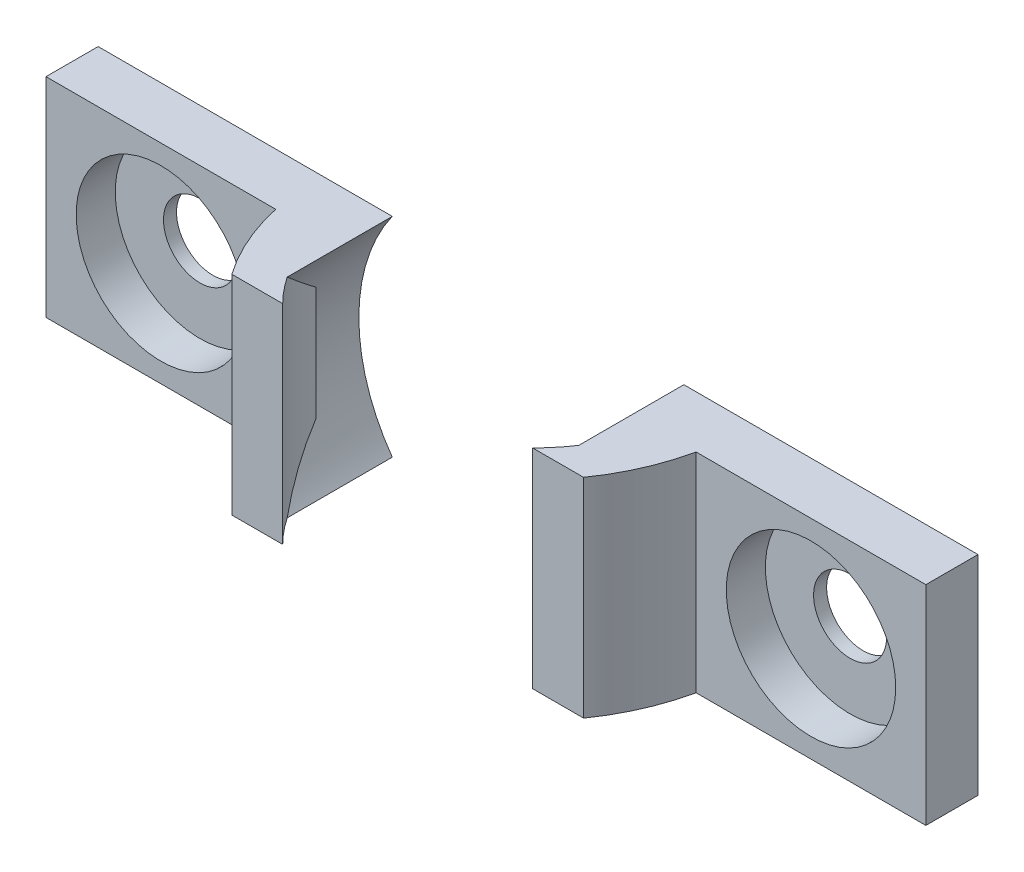
SolidWorks part; units mm, degrees
ref_plane "Alzado" through (0, 0, 0) normal (0, 0, 1) x (1, 0, 0)
ref_plane "Planta" through (0, 0, 0) normal (0, 1, 0) x (1, 0, 0)
ref_plane "Vista lateral" through (0, 0, 0) normal (1, 0, 0) x (0, 0, -1)
sketch "Croquis1" plane through (0, 0, 0) normal (0, 0, 1) x (1, 0, 0)
  line L0 (-52.0193, 52.8694) -> (-52.0193, 39.1194) construction
  line L1 (-58.8943, 45.9944) -> (-45.1443, 45.9944) construction
  line L2 (-57.6108, 41.9944) -> (-46.4277, 41.9944)
  line L3 (-57.6108, 49.9944) -> (-46.4277, 49.9944)
  line L4 (-58.8943, 49.9944) -> (-45.1443, 49.9944) construction
  line L5 (-58.8943, 41.9944) -> (-45.1443, 41.9944) construction
  line L6 (-57.6108, 41.9944) -> (-68.8943, 41.9944)
  line L7 (-68.8943, 41.9944) -> (-68.8943, 49.9944)
  line L9 (-68.8943, 49.9944) -> (-57.6108, 49.9944)
  line L10 (-46.4277, 41.9944) -> (-35.1443, 41.9944)
  line L11 (-35.1443, 41.9944) -> (-35.1443, 49.9944)
  line L12 (-35.1443, 49.9944) -> (-46.4277, 49.9944)
  circle A0 centre (-52.0193, 45.9944) radius 6.875 construction
  circle A1 centre (-52.0193, 45.9944) radius 6.875
  dimension "D3" = 10
  dimension "D1" = 4
  dimension "D2" = 4
extrude "Saliente-Extruir1" add sketch "Croquis1" along normal blind 2 contours A1 L9 L7 L6 | A1 L10 L11 L12
ref_plane "Plano1" through (0, 45.9944, 0) normal (0, -1, 0) x (-1, 0, 0)
sketch "Croquis2" plane through (0, 45.9944, 0) normal (0, -1, 0) x (-1, 0, 0)
  line L0 (35.1443, -2) -> (46.4277, -2) construction
  line L1 (43.957, -2) -> (45.5001, -2)
  line L2 (68.8943, -2) -> (57.6108, -2) construction
  line L3 (60.0815, -2) -> (58.5385, -2)
  line L4 (52.0193, -7) -> (46.0193, -7)
  line L5 (58.7646, -5) -> (56.8151, -5)
  line L6 (52.0193, 1.75) -> (52.0193, -1.5) construction
  line L7 (45.2739, -5) -> (47.2234, -5)
  line L8 (68.8943, 0) -> (57.6108, 0) construction
  line L9 (68.8943, 0) -> (57.6108, 0)
  circle A2 centre (52.0193, -0.25) radius 8.25
  circle A6 centre (52.0193, -0.25) radius 6.75
  dimension "D2" = 3
  dimension "D4" = 13.5
  dimension "D5" = 7
  dimension "D1" = 1.5
extrude "Saliente-Extruir2" add sketch "Croquis2" along normal mid plane 8
sketch "Croquis3" plane through (0, 0, 2) normal (0, 0, 1) x (1, 0, 0)
  line L2 (-58.5385, 49.9944) -> (-58.5385, 48.1774)
  line L3 (-57.6108, 49.9944) -> (-58.5385, 49.9944)
  line L5 (-57.6108, 49.9944) -> (-58.5385, 49.9944)
  line L7 (-58.5385, 49.9944) -> (-58.5385, 48.1774)
  arc A1 (-57.6108, 49.9944) -> (-58.5385, 48.1774) centre (-52.0193, 45.9944) ccw
  arc A2 (-57.6108, 49.9944) -> (-58.5385, 48.1774) centre (-52.0193, 45.9944) ccw
  dimension "D1" = 0
extrude "Saliente-Extruir3" add sketch "Croquis3" along normal up to next
sketch "Croquis4" plane through (0, 0, 2) normal (0, 0, 1) x (1, 0, 0)
  line L2 (-45.5001, 48.1774) -> (-45.5001, 49.9944)
  line L3 (-45.5001, 49.9944) -> (-46.4277, 49.9944)
  line L5 (-45.5001, 49.9944) -> (-46.4277, 49.9944)
  line L7 (-45.5001, 48.1774) -> (-45.5001, 49.9944)
  arc A1 (-45.5001, 48.1774) -> (-46.4277, 49.9944) centre (-52.0193, 45.9944) ccw
  arc A2 (-45.5001, 48.1774) -> (-46.4277, 49.9944) centre (-52.0193, 45.9944) ccw
  dimension "D1" = 0
extrude "Saliente-Extruir4" add sketch "Croquis4" along normal up to next
sketch "Croquis5" plane through (0, 0, 2) normal (0, 0, 1) x (1, 0, 0)
  line L2 (-58.5385, 43.8114) -> (-58.5385, 41.9944)
  line L3 (-58.5385, 41.9944) -> (-57.6108, 41.9944)
  line L5 (-58.5385, 41.9944) -> (-57.6108, 41.9944)
  line L7 (-58.5385, 43.8114) -> (-58.5385, 41.9944)
  arc A1 (-58.5385, 43.8114) -> (-57.6108, 41.9944) centre (-52.0193, 45.9944) ccw
  arc A2 (-58.5385, 43.8114) -> (-57.6108, 41.9944) centre (-52.0193, 45.9944) ccw
  dimension "D1" = 0
extrude "Saliente-Extruir5" add sketch "Croquis5" along normal up to next
sketch "Croquis6" plane through (0, 0, 2) normal (0, 0, 1) x (1, 0, 0)
  line L2 (-46.4277, 41.9944) -> (-45.5001, 41.9944)
  line L3 (-45.5001, 41.9944) -> (-45.5001, 43.8114)
  line L4 (-46.4277, 41.9944) -> (-45.5001, 41.9944)
  line L7 (-45.5001, 41.9944) -> (-45.5001, 43.8114)
  arc A1 (-46.4277, 41.9944) -> (-45.5001, 43.8114) centre (-52.0193, 45.9944) ccw
  arc A2 (-46.4277, 41.9944) -> (-45.5001, 43.8114) centre (-52.0193, 45.9944) ccw
  dimension "D1" = 0
extrude "Saliente-Extruir6" add sketch "Croquis6" along normal up to next
sketch "Croquis7" plane through (0, 0, 2) normal (0, 0, 1) x (1, 0, 0)
  line L0 (-68.8943, 49.9944) -> (-60.0815, 41.9944) construction
  line L1 (-60.0815, 49.9944) -> (-68.8943, 41.9944) construction
  line L2 (-43.957, 49.9944) -> (-35.1443, 41.9944) construction
  line L3 (-35.1443, 49.9944) -> (-43.957, 41.9944) construction
  circle A0 centre (-64.4879, 45.9944) radius 3.25
  circle A1 centre (-39.5506, 45.9944) radius 3.25
  dimension "D1" = 6.5
  dimension "D2" = 6.5
extrude "Cortar-Extruir1" cut sketch "Croquis7" against normal blind 1.5
sketch "Croquis8" plane through (0, 0, 0.5) normal (0, 0, 1) x (1, 0, 0)
  line L0 (-68.8943, 41.9944) -> (-68.8943, 49.9944) construction
  circle A0 centre (-64.4879, 45.9944) radius 1.4
  circle A1 centre (-39.5506, 45.9944) radius 1.4
  dimension "D1" = 2.8
  dimension "D2" = 2.8
extrude "Cortar-Extruir2" cut sketch "Croquis8" against normal up to next
